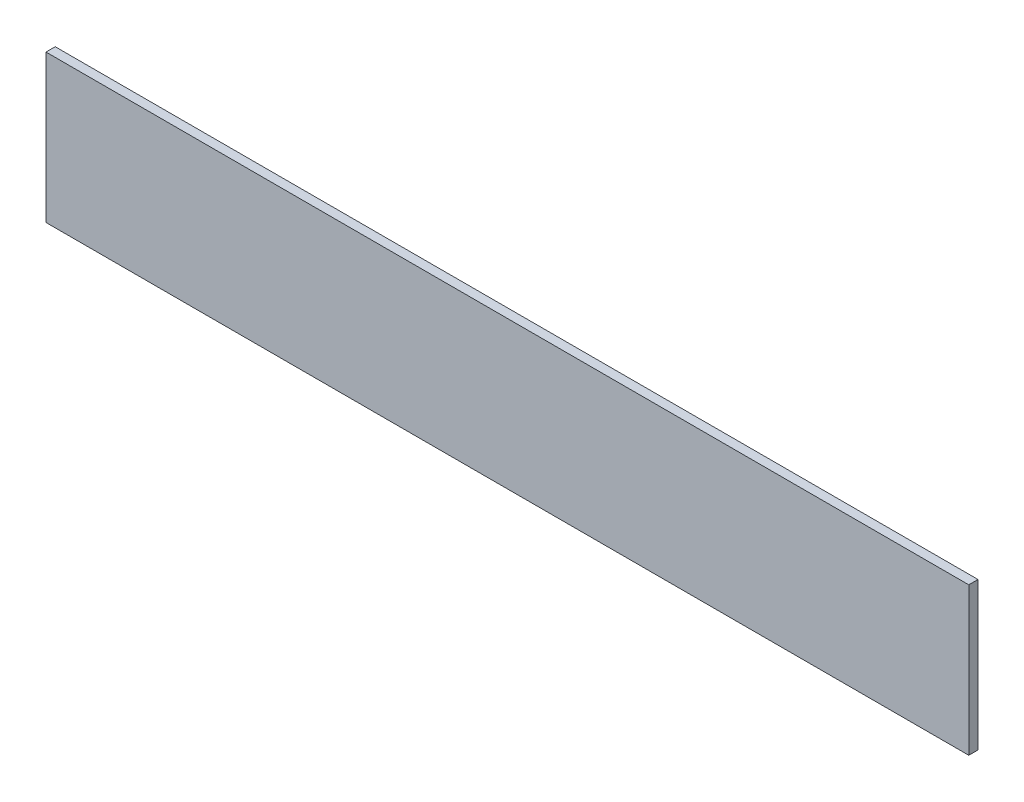
SolidWorks part; units mm, degrees
ref_plane "Front Plane" through (0, 0, 0) normal (0, 0, 1) x (1, 0, 0)
ref_plane "Top Plane" through (0, 0, 0) normal (0, 1, 0) x (1, 0, 0)
ref_plane "Right Plane" through (0, 0, 0) normal (1, 0, 0) x (0, 0, -1)
sketch "Sketch1" plane through (0, 0, 0) normal (0, 0, 1) x (1, 0, 0)
  line L1 (-635, -101.6) -> (635, -101.6)
  line L2 (-635, -101.6) -> (-635, 101.6)
  line L3 (-635, 101.6) -> (635, 101.6)
  line L4 (635, -101.6) -> (635, 101.6)
  line L5 (-635, -101.6) -> (635, 101.6) construction
  line L6 (-635, 101.6) -> (635, -101.6) construction
  point P0 (0, 0)
  dimension "D1" = 203.2
  dimension "D2" = 1270
extrude "Boss-Extrude1" add sketch "Sketch1" along normal blind 12.7
